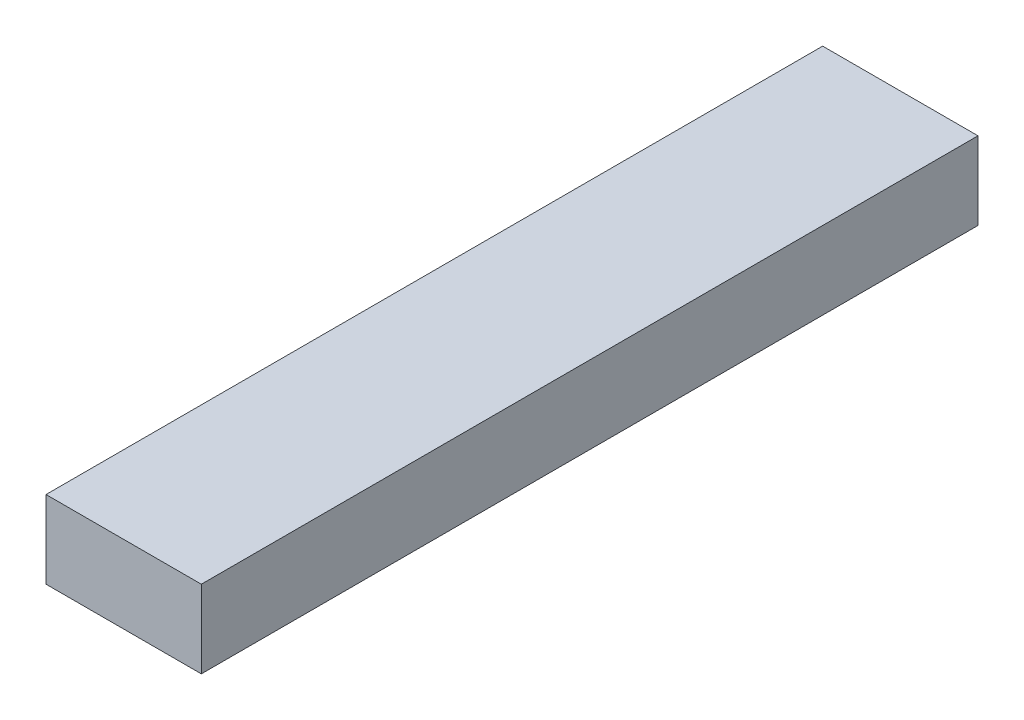
SolidWorks part; units mm, degrees
ref_plane "Front Plane" through (0, 0, 0) normal (0, 0, 1) x (1, 0, 0)
ref_plane "Top Plane" through (0, 0, 0) normal (0, 1, 0) x (1, 0, 0)
ref_plane "Right Plane" through (0, 0, 0) normal (1, 0, 0) x (0, 0, -1)
sketch "Sketch1" plane through (0, 0, 0) normal (0, 1, 0) x (1, 0, 0)
  line L0 (-10, 50) -> (10, -50) construction
  line L1 (-10, 50) -> (10, 50)
  line L2 (-10, 50) -> (-10, -50)
  line L3 (-10, -50) -> (10, -50)
  line L4 (10, 50) -> (10, -50)
  dimension "D1" = 20
  dimension "D2" = 100
extrude "Boss-Extrude1" add sketch "Sketch1" along normal blind 10
